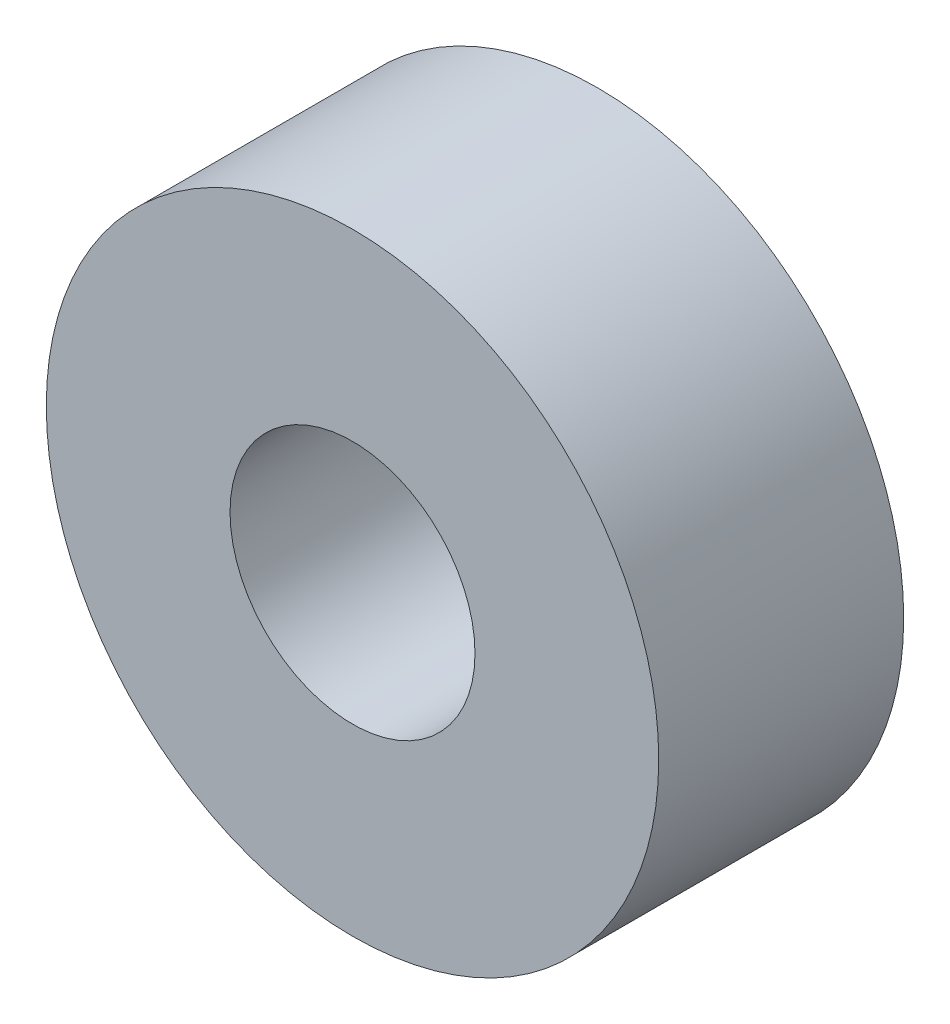
SolidWorks part; units mm, degrees
material "201 Annealed Stainless Steel (SS)"
ref_plane "Front Plane" through (0, 0, 0) normal (0, 0, 1) x (1, 0, 0)
ref_plane "Top Plane" through (0, 0, 0) normal (0, 1, 0) x (1, 0, 0)
ref_plane "Right Plane" through (0, 0, 0) normal (1, 0, 0) x (0, 0, -1)
sketch "Sketch1" plane through (0, 0, 0) normal (0, 0, 1) x (1, 0, 0)
  circle A0 centre (0, 0) radius 2
  circle A1 centre (0, 0) radius 5
  dimension "D1" = 10
  dimension "D2" = 4
extrude "Boss-Extrude1" add sketch "Sketch1" along normal blind 4
